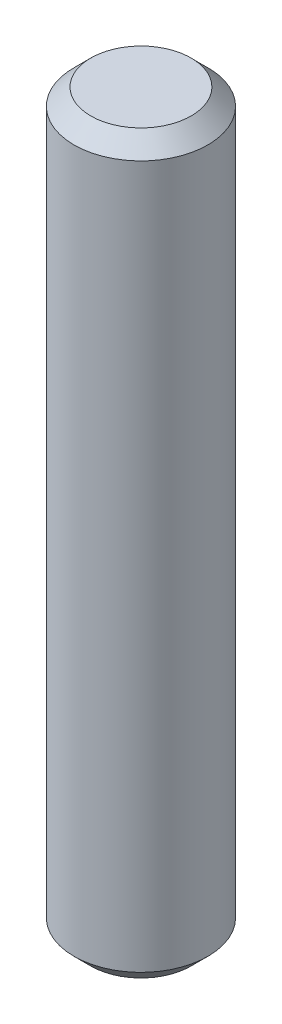
SolidWorks part; units mm, degrees
ref_plane "Front Plane" through (0, 0, 0) normal (0, 0, 1) x (1, 0, 0)
ref_plane "Top Plane" through (0, 0, 0) normal (0, 1, 0) x (1, 0, 0)
ref_plane "Right Plane" through (0, 0, 0) normal (1, 0, 0) x (0, 0, -1)
sketch "Sketch1" plane through (0, 0, 0) normal (0, 1, 0) x (1, 0, 0)
  circle A0 centre (0, 0) radius 2
  dimension "D1" = 4
extrude "Boss-Extrude1" add sketch "Sketch1" along normal blind 22
chamfer "Chamfer1" distance 0.5 angle 45 2 edges at (0, 0, 2) (0, 22, 2)
